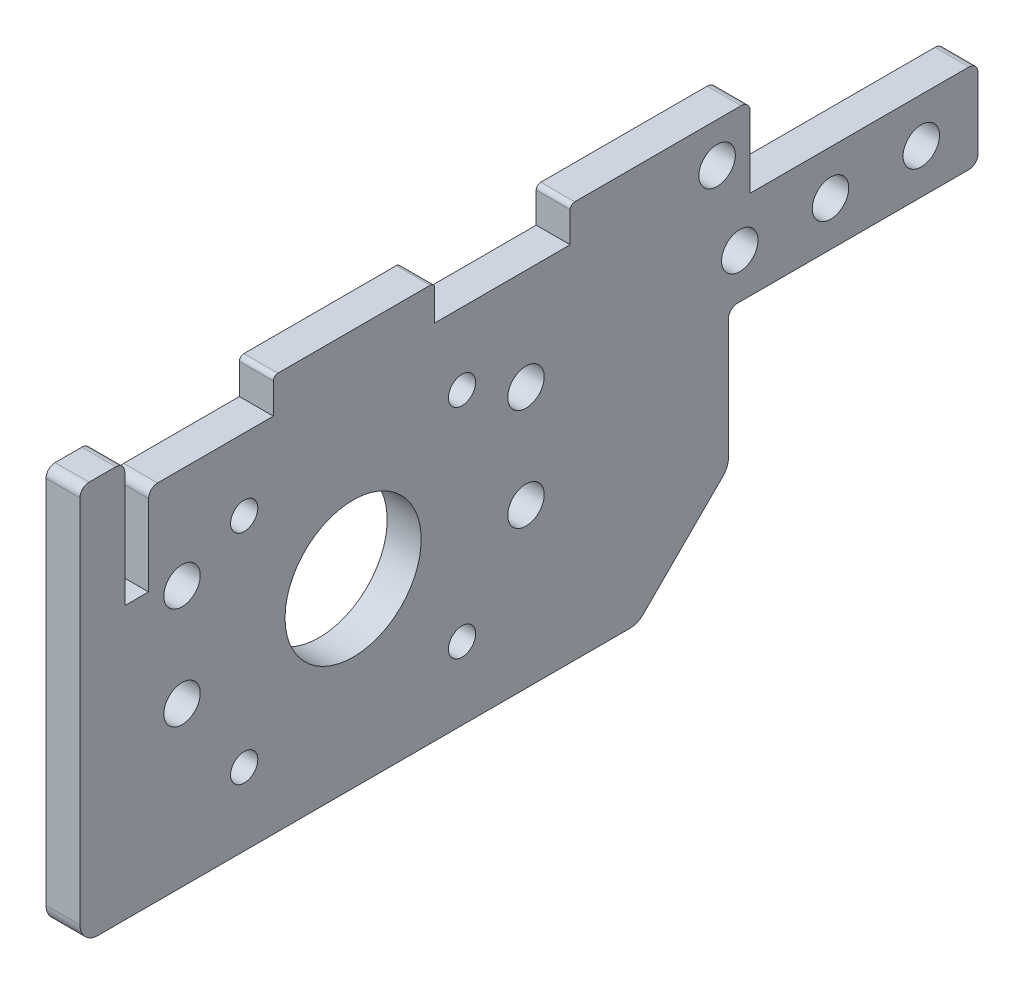
SolidWorks part; units mm, degrees
material "AISI Type A2 Tool Steel"
ref_plane "Front Plane" through (0, 0, 0) normal (0, 0, 1) x (1, 0, 0)
ref_plane "Top Plane" through (0, 0, 0) normal (0, 1, 0) x (1, 0, 0)
ref_plane "Right Plane" through (0, 0, 0) normal (1, 0, 0) x (0, 0, -1)
sketch "Top Layout" plane through (0, 0, 0) normal (0, 1, 0) x (1, 0, 0)
  line L0 (-114.046, -123.825) -> (-104.775, -123.825) construction
  line L1 (-104.775, -142.875) -> (-101.6, -142.875)
  line L2 (-104.775, -142.875) -> (-104.775, -104.775)
  line L3 (-104.775, -104.775) -> (-101.6, -104.775)
  line L4 (-101.6, -142.875) -> (-101.6, -104.775)
  line L5 (-104.775, -142.875) -> (-101.6, -104.775) construction
  line L6 (-104.775, -104.775) -> (-101.6, -142.875) construction
  line L7 (-19.05, -105.8164) -> (-101.6, -105.8164)
  line L8 (-19.05, -105.8164) -> (-19.05, -141.8336)
  line L9 (-19.05, -141.8336) -> (-101.6, -141.8336)
  line L10 (-101.6, -105.8164) -> (-101.6, -141.8336)
  line L11 (-19.05, -105.8164) -> (-101.6, -141.8336) construction
  line L12 (-19.05, -141.8336) -> (-101.6, -105.8164) construction
  line L13 (-133.096, -85.725) -> (-114.046, -85.725)
  line L14 (-133.096, -85.725) -> (-133.096, -161.925)
  line L15 (-133.096, -161.925) -> (-114.046, -161.925)
  line L16 (-114.046, -85.725) -> (-114.046, -161.925)
  line L17 (-133.096, -85.725) -> (-114.046, -161.925) construction
  line L18 (-133.096, -161.925) -> (-114.046, -85.725) construction
  line L19 (-104.775, -123.825) -> (0, -123.825) construction
  line L20 (0, -123.825) -> (0, 0) construction
  line L21 (-52.3528, -40.1717) -> (0, 0) construction
  line L22 (-70.6449, -16.3328) -> (-18.2922, 23.8388)
  line L23 (-34.0606, -64.0105) -> (18.2922, -23.8388)
  line L24 (-30.9251, 40.3023) -> (-122.2248, -29.7544)
  line L25 (-153.9748, -53.975) -> (-153.9748, -123.825)
  line L26 (-109.5248, -162.052) -> (109.5248, -162.052)
  line L27 (0, -162.052) -> (0, -123.825) construction
  line L28 (-109.5248, -162.052) -> (-109.5248, -20.0093) construction
  line L29 (-104.775, -142.875) -> (-104.775, -152.527)
  line L30 (-104.775, -152.527) -> (104.775, -152.527)
  line L31 (104.775, -104.775) -> (101.6, -104.775)
  line L32 (-144.4498, -73.025) -> (-109.5248, -73.025)
  line L33 (-144.4498, -73.025) -> (-144.4498, -123.825)
  line L34 (-144.4498, -123.825) -> (-109.5248, -123.825) construction
  line L35 (-109.5248, -73.025) -> (-109.5248, -162.052)
  line L36 (-144.4498, -73.025) -> (-109.5248, -123.825) construction
  line L37 (-144.4498, -123.825) -> (-109.5248, -73.025) construction
  line L38 (101.6, -142.875) -> (101.6, -104.775)
  line L39 (104.775, -142.875) -> (101.6, -142.875)
  line L40 (104.775, -142.875) -> (104.775, -104.775)
  line L41 (104.775, -142.875) -> (104.775, -152.527)
  line L42 (109.5248, -162.052) -> (109.5248, -20.0093) construction
  line L43 (30.9251, 40.3023) -> (122.2248, -29.7544)
  line L45 (19.05, -141.8336) -> (101.6, -141.8336)
  line L46 (101.6, -105.8164) -> (101.6, -141.8336)
  line L47 (19.05, -105.8164) -> (101.6, -105.8164)
  line L48 (19.05, -105.8164) -> (19.05, -141.8336)
  line L49 (133.096, -161.925) -> (114.046, -161.925)
  line L50 (114.046, -85.725) -> (114.046, -161.925)
  line L51 (133.096, -85.725) -> (114.046, -85.725)
  line L52 (133.096, -85.725) -> (133.096, -161.925)
  line L53 (144.4498, -123.825) -> (109.5248, -123.825) construction
  line L54 (109.5248, -73.025) -> (109.5248, -162.052)
  line L55 (144.4498, -73.025) -> (109.5248, -73.025)
  line L56 (144.4498, -73.025) -> (144.4498, -123.825)
  line L57 (-109.5248, -123.825) -> (-109.5248, -162.052) construction
  line L62 (-153.9748, -53.975) -> (-122.2248, -53.975)
  line L63 (-122.2248, -53.975) -> (-122.2248, -29.7544)
  line L64 (-144.4498, -123.825) -> (-153.9748, -123.825)
  line L65 (153.9748, -53.975) -> (153.9748, -123.825)
  line L66 (109.5248, -123.825) -> (109.5248, -162.052) construction
  line L67 (144.4498, -123.825) -> (153.9748, -123.825)
  line L68 (122.2248, -29.7544) -> (122.2248, -53.975)
  line L73 (-104.775, -104.775) -> (-104.775, -16.3647) construction
  line L74 (-95.25, -162.052) -> (-95.25, -9.0559) construction
  line L75 (-109.5248, -162.052) -> (-109.5248, -123.825) construction
  line L76 (109.5248, -162.052) -> (109.5248, -123.825) construction
  line L77 (122.2248, -53.975) -> (153.9748, -53.975)
  line L83 (104.775, -155.5496) -> (-104.775, -155.5496) construction
  line L88 (95.25, -162.052) -> (95.25, -9.0559) construction
  line L89 (104.775, -104.775) -> (104.775, -16.3647) construction
  line L92 (-104.775, -152.527) -> (-104.775, -162.052) construction
  line L93 (-14.605, -76.327) -> (14.605, -76.327)
  line L94 (-14.605, -76.327) -> (-14.605, -152.527)
  line L95 (-14.605, -152.527) -> (14.605, -152.527)
  line L96 (14.605, -76.327) -> (14.605, -152.527)
  line L97 (-14.605, -76.327) -> (14.605, -152.527) construction
  line L98 (-14.605, -152.527) -> (14.605, -76.327) construction
  line L99 (104.775, -152.527) -> (104.775, -162.052) construction
  line L100 (-19.05, -105.8164) -> (0, -105.8164) construction
  line L107 (0, -105.8164) -> (19.05, -105.8164) construction
  line L108 (104.775, -123.825) -> (114.046, -123.825) construction
  circle A0 centre (0, 0) radius 114.3
  circle A1 centre (0, 0) radius 6.35
  circle A2 centre (-52.3528, -40.1717) radius 17.8
  circle A3 centre (0, 0) radius 30.0482
  circle A4 centre (-52.3528, -40.1717) radius 30.0482
  arc A5 (-30.9251, 40.3023) -> (30.9251, 40.3023) centre (0, 0) cw
  point P2 (-103.1875, -123.825)
  point P7 (-60.325, -123.825)
  point P12 (-123.571, -123.825)
  point P30 (-126.9873, -98.425)
  point P35 (0, -114.427)
  point P53 (0, -152.527)
  dimension "D1" = 35.6
  dimension "D2" = 12.7
  dimension "D3" = 228.6
  dimension "D11" = 60.0964
  dimension "D12" = 50.8
  dimension "D14" = 52.5
  dimension "D4" = 3.175
  dimension "D5" = 19.05
  dimension "D6" = 76.2
  dimension "D7" = 82.55
  dimension "D8" = 38.1
  dimension "D9" = 104.775
  dimension "D10" = 18.0086
  dimension "D13" = 9.525
  dimension "D15" = 4.7498
  dimension "D16" = 9.525
  dimension "D17" = 9.652
  dimension "D18" = 50.8
  dimension "D19" = 12.446
  dimension "D20" = 65.9892
  dimension "D21" = 19.05
  dimension "D22" = 34.925
  dimension "D23" = 123.825
  dimension "D24" = 12.7
  dimension "D25" = 9.525
  dimension "D26" = 29.21
  dimension "D27" = 76.2
  dimension "D28" = 3.0226
sketch "Side Layout" plane through (0, 0, 0) normal (1, 0, 0) x (0, 0, -1)
  line L0 (0, -38.1) -> (0, 33.7344) construction
  line L1 (-114.3, -20.955) -> (114.3, -20.955)
  line L2 (-114.3, -20.955) -> (-114.3, -33.655)
  line L3 (-114.3, -33.655) -> (114.3, -33.655)
  line L4 (114.3, -20.955) -> (114.3, -33.655)
  line L5 (-114.3, -20.955) -> (114.3, -33.655) construction
  line L6 (-114.3, -33.655) -> (114.3, -20.955) construction
  line L7 (-9.525, -32.9406) -> (9.525, -32.9406)
  line L8 (-9.525, -32.9406) -> (-9.525, -38.1)
  line L9 (-9.525, -38.1) -> (9.525, -38.1)
  line L10 (9.525, -32.9406) -> (9.525, -38.1)
  line L11 (-9.525, -32.9406) -> (9.525, -38.1) construction
  line L12 (-9.525, -38.1) -> (9.525, -32.9406) construction
  line L13 (-11.9126, -29.3338) -> (11.9126, -29.3338)
  line L14 (-11.9126, -29.3338) -> (-11.9126, -32.9406)
  line L15 (-11.9126, -32.9406) -> (11.9126, -32.9406)
  line L16 (11.9126, -29.3338) -> (11.9126, -32.9406)
  line L17 (-11.9126, -29.3338) -> (11.9126, -32.9406) construction
  line L18 (-11.9126, -32.9406) -> (11.9126, -29.3338) construction
  line L19 (-6.35, -32.9406) -> (6.35, -32.9406)
  line L20 (-6.35, -32.9406) -> (-6.35, 33.7344)
  line L21 (-6.35, 33.7344) -> (6.35, 33.7344)
  line L22 (6.35, -32.9406) -> (6.35, 33.7344)
  line L23 (-6.35, -32.9406) -> (6.35, 33.7344) construction
  line L24 (-6.35, 33.7344) -> (6.35, -32.9406) construction
  line L25 (-162.052, 0) -> (-123.825, 0) construction
  line L26 (114.3, -33.655) -> (114.3, 0) construction
  line L27 (-142.875, 19.05) -> (-104.775, 19.05)
  line L28 (-40.1717, -9.525) -> (-40.1717, 5.4) construction
  line L29 (-142.875, 19.05) -> (-142.875, -19.05)
  line L30 (-142.875, -19.05) -> (-104.775, -19.05)
  line L31 (-104.775, 19.05) -> (-104.775, -19.05)
  line L32 (-142.875, 19.05) -> (-104.775, -19.05) construction
  line L33 (-142.875, -19.05) -> (-104.775, 19.05) construction
  line L34 (-130.175, -38.1) -> (-117.9516, -38.1) construction
  line L35 (-57.9717, -14.6) -> (-22.3717, -14.6)
  line L36 (-30.0482, -2.794) -> (30.0482, -2.794)
  line L37 (-30.0482, -2.794) -> (-30.0482, -20.955)
  line L38 (-30.0482, -20.955) -> (30.0482, -20.955)
  line L39 (30.0482, -2.794) -> (30.0482, -20.955)
  line L40 (-30.0482, -2.794) -> (30.0482, -20.955) construction
  line L41 (-30.0482, -20.955) -> (30.0482, -2.794) construction
  line L42 (-30.0482, -2.794) -> (-30.0482, 0) construction
  line L43 (-123.825, 0) -> (0, 0) construction
  line L44 (-57.9717, -14.6) -> (-57.9717, 25.4)
  line L45 (-57.9717, 25.4) -> (-22.3717, 25.4)
  line L46 (-22.3717, -14.6) -> (-22.3717, 25.4)
  line L47 (-19.05, 0) -> (19.05, 0)
  line L48 (-19.05, 0) -> (-19.05, -1.9812)
  line L49 (-19.05, -1.9812) -> (19.05, -1.9812)
  line L50 (19.05, 0) -> (19.05, -1.9812)
  line L51 (-19.05, 0) -> (19.05, -1.9812) construction
  line L52 (-19.05, -1.9812) -> (19.05, 0) construction
  line L53 (-70.2199, -3.175) -> (-10.1235, -3.175)
  line L54 (-70.2199, -3.175) -> (-70.2199, -15.875)
  line L55 (-70.2199, -15.875) -> (-10.1235, -15.875)
  line L56 (-10.1235, -3.175) -> (-10.1235, -15.875)
  line L57 (-70.2199, -3.175) -> (-10.1235, -15.875) construction
  line L58 (-70.2199, -15.875) -> (-10.1235, -3.175) construction
  line L59 (-40.1717, -9.525) -> (-40.1717, 0) construction
  line L60 (-57.9717, -14.6) -> (-22.3717, 25.4) construction
  line L61 (-57.9717, 25.4) -> (-22.3717, -14.6) construction
  line L62 (-22.3717, 0) -> (-57.9717, 0) construction
  line L63 (-137.8162, 0) -> (-123.825, -13.9912) construction
  line L64 (-139.065, 15.24) -> (-108.585, 15.24) construction
  line L65 (-139.065, 15.24) -> (-139.065, -15.24) construction
  line L66 (-139.065, -15.24) -> (-108.585, -15.24) construction
  line L67 (-108.585, 15.24) -> (-108.585, -15.24) construction
  line L68 (-139.065, 15.24) -> (-108.585, -15.24) construction
  line L69 (-139.065, -15.24) -> (-108.585, 15.24) construction
  line L70 (-137.8162, 0) -> (-123.825, 13.9912) construction
  line L71 (-123.825, -13.9912) -> (-109.8338, 0) construction
  line L72 (-123.825, 13.9912) -> (-109.8338, 0) construction
  line L73 (-137.8162, 0) -> (-109.8338, 0) construction
  line L74 (-123.825, -13.9912) -> (-123.825, 13.9912) construction
  line L75 (-6.35, 17.8594) -> (6.35, 17.8594)
  line L76 (114.3, 0) -> (-114.3, 0) construction
  line L77 (-22.3717, 19.05) -> (-6.35, 19.05) construction
  line L78 (-123.825, 38.1) -> (-97.9206, 38.1) construction
  line L79 (-19.05, -3.5814) -> (19.05, -3.5814)
  line L80 (-19.05, -3.5814) -> (-19.05, -1.9812)
  line L81 (-19.05, -1.9812) -> (19.05, -1.9812)
  line L82 (19.05, -3.5814) -> (19.05, -1.9812)
  line L83 (-19.05, -3.5814) -> (19.05, -1.9812) construction
  line L84 (-19.05, -1.9812) -> (19.05, -3.5814) construction
  line L85 (-8.7376, -16.7608) -> (8.7376, -16.7608)
  line L86 (-8.7376, -16.7608) -> (-8.7376, -29.3338)
  line L87 (-8.7376, -29.3338) -> (8.7376, -29.3338)
  line L88 (8.7376, -16.7608) -> (8.7376, -29.3338)
  line L89 (-8.7376, -16.7608) -> (8.7376, -29.3338) construction
  line L90 (-8.7376, -29.3338) -> (8.7376, -16.7608) construction
  line L91 (-8.7376, -3.5814) -> (8.7376, -3.5814)
  line L92 (-8.7376, -3.5814) -> (-8.7376, -16.1544)
  line L93 (-8.7376, -16.1544) -> (8.7376, -16.1544)
  line L94 (8.7376, -3.5814) -> (8.7376, -16.1544)
  line L95 (-8.7376, -3.5814) -> (8.7376, -16.1544) construction
  line L96 (-8.7376, -16.1544) -> (8.7376, -3.5814) construction
  circle A0 centre (-123.825, 0) radius 18.0086
  circle A1 centre (-123.825, 0) radius 38.1
  circle A2 centre (-139.065, 15.24) radius 1.905
  circle A3 centre (-108.585, 15.24) radius 1.905
  circle A4 centre (-108.585, -15.24) radius 1.905
  circle A5 centre (-139.065, -15.24) radius 1.905
  circle A6 centre (-137.8162, 0) radius 1.6002
  circle A7 centre (-123.825, 13.9912) radius 1.6002
  circle A8 centre (-109.8338, 0) radius 1.6002
  circle A9 centre (-123.825, -13.9912) radius 1.6002
  point P0 (0, -27.305)
  point P6 (0, -31.1372)
  point P7 (0, -35.5203)
  point P21 (0, 0.3969)
  point P32 (0, -11.8745)
  point P43 (0, -0.9906)
  point P55 (-40.1717, -9.525)
  point P72 (-40.1717, 5.4)
  point P88 (0, -23.0473)
  point P93 (0, -2.7813)
  point P102 (0, -9.8679)
  dimension "D17" = 3.81
  dimension "D18" = 3.2004
  dimension "D1" = 12.7
  dimension "D2" = 5.1594
  dimension "D3" = 19.05
  dimension "D4" = 3.6068
  dimension "D5" = 23.8252
  dimension "D6" = 12.7
  dimension "D7" = 18.161
  dimension "D8" = 1.9812
  dimension "D9" = 12.7
  dimension "D10" = 40
  dimension "D11" = 25.4
  dimension "D12" = 50.8
  dimension "D13" = 41.275
  dimension "D14" = 30.48
  dimension "D15" = 4.445
  dimension "D16" = 19.7866
  dimension "D19" = 15.875
  dimension "D20" = 6.35
  dimension "D21" = 38.1
  dimension "D22" = 1.6002
  dimension "D23" = 38.1
  dimension "D24" = 17.4752
  dimension "D25" = 12.573
ref_plane "Plane1" through (0, 25.4, 0) normal (0, 1, 0) x (1, 0, 0)
sketch "Sketch3" plane through (0, 25.4, 0) normal (0, 1, 0) x (1, 0, 0)
  line L0 (-104.775, -36.3747) -> (-30.9251, 20.2924)
  line L1 (-104.775, -104.775) -> (-104.775, -16.3647) construction
  line L2 (0, -200130.175) -> (0, 199882.0484) construction
  line L3 (-30.9251, 40.3023) -> (-122.2248, -29.7544) construction
  line L5 (-104.775, -36.3747) -> (-104.775, -77.6497)
  line L6 (-92.075, -77.6497) -> (-104.775, -77.6497)
  line L7 (30.9251, 20.2924) -> (104.775, -36.3747)
  line L8 (104.775, -77.6497) -> (92.075, -77.6497)
  line L9 (104.775, -36.3747) -> (104.775, -77.6497)
  line L11 (104.775, -104.775) -> (104.775, -16.3647) construction
  line L12 (30.9251, 40.3023) -> (122.2248, -29.7544) construction
  line L13 (92.075, -74.6536) -> (24.1423, -22.5271)
  line L14 (-32.2514, -66.3682) -> (20.1013, -26.1965)
  line L15 (-30.9251, 20.2924) -> (0, 44.022)
  line L16 (0, 44.022) -> (30.9251, 20.2924)
  line L17 (-92.075, -77.6497) -> (-92.075, -73.1917)
  line L19 (-92.075, -73.1917) -> (-52.3528, -73.1917)
  line L20 (92.075, -74.6536) -> (92.075, -77.6497)
  circle A0 centre (-52.3528, -40.1717) radius 17.8 construction
  circle A1 centre (-52.3528, -40.1717) radius 17.8
  circle A2 centre (0, 0) radius 6.35
  circle A3 centre (0, 0) radius 6.35 construction
  arc A4 (-52.3528, -73.1917) -> (-32.2514, -66.3682) centre (-52.3528, -40.1717) ccw
  arc A5 (20.1013, -26.1965) -> (24.1423, -22.5271) centre (0, 0) ccw
  arc A6 (30.9251, 20.2924) -> (-30.9251, 20.2924) centre (0, -20.01) ccw construction
  point P28 (0, 44.022)
  dimension "D1" = 33.02
  dimension "D5" = 50.8
  dimension "D2" = 41.275
  dimension "D3" = 34.925
  dimension "D4" = 12.7
  dimension "D6" = 38.1
ref_plane "Plane3" through (-104.775, 0, 0) normal (-1, 0, 0) x (0, 0, 1)
sketch "Sketch6" plane through (-104.775, 0, 0) normal (-1, 0, 0) x (0, 0, 1)
  line L0 (162.052, -25.4) -> (162.052, 25.4)
  line L1 (162.052, 25.4) -> (77.6497, 25.4)
  line L2 (36.3747, 25.4) -> (77.6497, 25.4) construction
  line L3 (147.7645, 11.1125) -> (162.052, 11.1125) construction
  line L4 (162.052, 0) -> (71.2997, 0) construction
  line L5 (77.6497, 25.4) -> (77.6497, 19.05)
  line L6 (77.6497, 19.05) -> (36.3747, 19.05)
  line L7 (36.3747, 19.05) -> (36.3747, 6.35)
  line L8 (36.3747, 6.35) -> (71.2997, 6.35)
  line L10 (99.6315, -3.175) -> (99.6315, 11.1125) construction
  line L11 (71.2997, -25.4) -> (162.052, -25.4)
  line L13 (71.2997, 6.35) -> (71.2997, -25.4)
  line L14 (152.527, -25.4) -> (152.527, 25.4) construction
  line L15 (99.6315, 11.1125) -> (99.6315, 25.4) construction
  line L16 (147.7645, 11.1125) -> (147.7645, 25.4) construction
  line L17 (94.869, -7.9375) -> (104.394, -7.9375) construction
  line L18 (94.869, -7.9375) -> (94.869, 25.4) construction
  line L19 (94.869, 25.4) -> (104.394, 25.4) construction
  line L20 (104.394, -7.9375) -> (104.394, 25.4) construction
  line L21 (94.869, -7.9375) -> (104.394, 25.4) construction
  line L22 (94.869, 25.4) -> (104.394, -7.9375) construction
  line L23 (147.7645, 11.1125) -> (147.7645, -3.175) construction
  line L24 (104.394, -7.9375) -> (123.825, -7.9375) construction
  line L25 (143.002, -7.9375) -> (152.527, -7.9375) construction
  line L26 (143.002, -7.9375) -> (143.002, 25.4) construction
  line L27 (143.002, 25.4) -> (152.527, 25.4) construction
  line L28 (152.527, -7.9375) -> (152.527, 25.4) construction
  line L29 (143.002, -7.9375) -> (152.527, 25.4) construction
  line L30 (143.002, 25.4) -> (152.527, -7.9375) construction
  line L31 (123.825, -7.9375) -> (152.527, -7.9375) construction
  line L32 (104.775, 19.05) -> (104.775, -19.05) construction
  line L34 (155.702, -25.4) -> (155.702, 25.4) construction
  circle A0 centre (109.8338, 0) radius 1.6002 construction
  circle A1 centre (123.825, 13.9912) radius 1.6002 construction
  circle A2 centre (137.8162, 0) radius 1.6002 construction
  circle A3 centre (123.825, -13.9912) radius 1.6002 construction
  circle A4 centre (109.8338, 0) radius 1.6002 construction
  circle A5 centre (123.825, 13.9912) radius 1.6002 construction
  circle A6 centre (137.8162, 0) radius 1.6002 construction
  circle A7 centre (123.825, -13.9912) radius 1.6002 construction
  circle A8 centre (123.825, 0) radius 18.0086 construction
  circle A9 centre (123.825, 0) radius 18.0086 construction
  circle A10 centre (123.825, 0) radius 9.525
  circle A11 centre (108.585, -15.24) radius 1.905 construction
  circle A12 centre (108.585, 15.24) radius 1.905 construction
  circle A13 centre (139.065, 15.24) radius 1.905 construction
  circle A14 centre (139.065, -15.24) radius 1.905 construction
  circle A15 centre (108.585, -15.24) radius 1.905
  circle A16 centre (108.585, 15.24) radius 1.905
  circle A17 centre (139.065, 15.24) radius 1.905
  circle A18 centre (139.065, -15.24) radius 1.905
  circle A19 centre (147.7645, 11.1125) radius 2.5527
  circle A26 centre (99.6315, 11.1125) radius 2.5527
  circle A27 centre (99.6315, -3.175) radius 2.5527
  circle A28 centre (147.7645, -3.175) radius 2.5527
  point P29 (0, 0)
  point P55 (99.6315, 8.7312)
  point P61 (147.7645, 8.7312)
  dimension "D4" = 19.05
  dimension "D7" = 5.1054
  dimension "D1" = 6.35
  dimension "D2" = 12.7
  dimension "D3" = 25.4
  dimension "D5" = 6.35
  dimension "D6" = 3.175
  dimension "D8" = 0.381
  dimension "D9" = 14.2875
  dimension "D10" = 9.525
  dimension "D12" = 33.3375
extrude "Side Plate Extrude" add sketch "Sketch6" along normal up to vertex (4.7498 mm away) up to point (-109.5248, 0, 73.025)
sketch "Sketch12" [suppressed] plane through (0, 19.05, 0) normal (0, 1, 0) x (1, 0, 0)
  line L0 (-104.775, -77.6497) -> (-104.775, -36.3747)
  line L1 (-104.775, -36.3747) -> (-92.075, -36.3747)
  line L3 (-92.075, -36.3747) -> (-92.075, -77.6497)
  line L5 (-92.075, -77.6497) -> (-104.775, -77.6497)
  line L6 (-98.425, -77.6497) -> (-98.425, -63.3622) construction
  line L7 (-98.425, -63.3622) -> (-98.425, -50.6622) construction
  line L8 (-98.425, -50.6622) -> (-98.425, -36.3747) construction
  line L10 (-98.425, -36.3747) -> (-104.775, -36.3747) construction
  circle A0 centre (-98.425, -63.3622) radius 2.5527
  circle A1 centre (-98.425, -50.6622) radius 2.5527
  dimension "D2" = 5.1054
  dimension "D1" = 12.7
  dimension "D3" = 12.7
sketch "Sketch15" plane through (-109.5248, 0, 0) normal (-1, 0, 0) x (0, 0, 1)
  line L0 (36.3747, 12.7) -> (44.3122, 12.7) construction
  line L1 (36.3747, 19.05) -> (36.3747, 6.35) construction
  line L2 (44.3122, 12.7) -> (57.0122, 12.7) construction
  line L3 (57.0122, 12.7) -> (69.7122, 12.7) construction
  line L4 (69.7122, 12.7) -> (77.6497, 12.7) construction
  line L5 (77.6497, 12.7) -> (77.6497, 19.05) construction
  circle A0 centre (44.3122, 12.7) radius 2.5527
  circle A1 centre (57.0122, 12.7) radius 2.5527
  circle A2 centre (69.7122, 12.7) radius 2.5527
  dimension "D1" = 5.1054
  dimension "D2" = 12.7
extrude "Custom Nutstrip Holes" cut sketch "Sketch15" against normal through all
ref_plane "Plane5" through (0, 0, 152.527) normal (0, 0, 1) x (1, 0, 0)
sketch "Sketch41" plane through (0, 0, 152.527) normal (0, 0, 1) x (1, 0, 0)
  line L0 (-104.775, -7.9375) -> (-104.775, 25.4) construction
  line L1 (-104.775, -7.9375) -> (-104.775, 12.7)
  line L2 (-104.775, -7.9375) -> (104.775, -7.9375)
  line L3 (104.775, -7.9375) -> (104.775, 12.7)
  line L4 (104.775, 25.4) -> (-104.775, 25.4)
  line L5 (0, -7.9375) -> (0, 25.4) construction
  line L6 (-104.775, 3.9624) -> (-100.0125, 3.9624) construction
  line L7 (-100.0125, 3.9624) -> (-100.0125, 25.4) construction
  line L8 (104.775, 3.9624) -> (100.0125, 3.9624) construction
  line L9 (100.0125, 3.9624) -> (100.0125, 25.4) construction
  line L10 (19.05, 20.6375) -> (23.8252, 20.6375) construction
  line L11 (19.05, 15.875) -> (78.5876, 15.875) construction
  line L12 (19.05, 15.875) -> (19.05, 25.4) construction
  line L13 (19.05, 25.4) -> (78.5876, 25.4) construction
  line L14 (78.5876, 15.875) -> (78.5876, 25.4) construction
  line L15 (19.05, 15.875) -> (78.5876, 25.4) construction
  line L16 (19.05, 25.4) -> (78.5876, 15.875) construction
  line L17 (23.8252, 20.6375) -> (38.1127, 20.6375) construction
  line L18 (38.1127, 20.6375) -> (52.4002, 20.6375) construction
  line L19 (52.4002, 20.6375) -> (66.6877, 20.6375) construction
  line L20 (-104.775, 25.4) -> (-112.395, 25.4)
  line L21 (-112.395, 25.4) -> (-112.395, 3.175)
  line L22 (-112.395, 3.175) -> (-109.5248, 3.175)
  line L23 (-109.5248, 3.175) -> (-109.5248, 12.7)
  line L24 (-109.5248, 12.7) -> (-104.775, 12.7)
  line L25 (-104.775, 12.7) -> (-104.775, 25.4) construction
  line L26 (104.775, 25.4) -> (112.395, 25.4)
  line L27 (112.395, 25.4) -> (112.395, 3.175)
  line L28 (112.395, 3.175) -> (109.5248, 3.175)
  line L29 (109.5248, 3.175) -> (109.5248, 12.7)
  line L30 (109.5248, 12.7) -> (104.775, 12.7)
  line L31 (104.775, 12.7) -> (104.775, 25.4) construction
  line L32 (-100.0125, 3.9624) -> (-87.3125, 3.9624) construction
  line L33 (-63.5, -1.5875) -> (0, -1.5875) construction
  line L34 (0, -1.5875) -> (63.5, -1.5875) construction
  line L35 (63.5, -1.5875) -> (63.5, -7.9375) construction
  circle A0 centre (-100.0125, 3.9624) radius 2.5527
  circle A1 centre (100.0125, 3.9624) radius 2.5527
  circle A2 centre (23.8252, 20.6375) radius 2.5527
  circle A3 centre (38.1127, 20.6375) radius 2.5527
  circle A4 centre (52.4002, 20.6375) radius 2.5527
  circle A5 centre (66.6877, 20.6375) radius 2.5527
  circle A6 centre (-66.6877, 20.6375) radius 2.5527
  circle A7 centre (-52.4002, 20.6375) radius 2.5527
  circle A8 centre (-38.1127, 20.6375) radius 2.5527
  circle A9 centre (-23.8252, 20.6375) radius 2.5527
  circle A10 centre (-87.3125, 3.9624) radius 2.5527
  circle A11 centre (87.3125, 3.9624) radius 2.5527
  circle A12 centre (-63.5, -1.5875) radius 2.5527
  circle A13 centre (63.5, -1.5875) radius 2.5527
  point P14 (48.8188, 20.6375)
  dimension "D3" = 5.1054
  dimension "D7" = 5.1054
  dimension "D1" = 21.4376
  dimension "D2" = 4.7625
  dimension "D4" = 9.525
  dimension "D5" = 59.5376
  dimension "D6" = 4.7752
  dimension "D8" = 14.2875
  dimension "D9" = 7.62
  dimension "D10" = 4.7498
  dimension "D11" = 12.7
  dimension "D12" = 9.525
  dimension "D13" = 19.05
  dimension "D14" = 12.7
  dimension "D15" = 6.35
  dimension "D16" = 63.5
sketch "Sketch43" plane through (-109.5248, 0, 0) normal (-1, 0, 0) x (0, 0, 1)
  line L1 (152.527, 12.7) -> (155.702, 12.7)
  line L2 (152.527, 12.7) -> (152.527, 25.4)
  line L3 (152.527, 25.4) -> (155.702, 25.4)
  line L4 (155.702, 12.7) -> (155.702, 25.4)
  line L5 (152.527, 12.7) -> (155.702, 25.4) construction
  line L6 (152.527, 25.4) -> (155.702, 12.7) construction
  line L7 (162.052, 25.4) -> (77.6497, 25.4) construction
  point P4 (154.1145, 19.05)
  dimension "D1" = 3.175
extrude "Cut-Extrude19" cut sketch "Sketch43" against normal through all
sketch "Sketch44" plane through (0, 25.4, 0) normal (0, 1, 0) x (1, 0, 0)
  line L0 (73.8315, -147.7645) -> (73.8315, -152.527) construction
  line L1 (92.075, -74.6536) -> (92.075, -77.6497) construction
  line L2 (-92.075, -77.6497) -> (-92.075, -73.1917) construction
  line L3 (0, -123.825) -> (0, 0) construction
  line L4 (-92.075, -73.1917) -> (-52.3528, -73.1917) construction
  line L5 (-104.775, -104.775) -> (-104.775, -16.3647) construction
  line L6 (-32.2514, -66.3682) -> (20.1013, -26.1965) construction
  line L21 (-104.775, -68.1247) -> (-104.775, -152.527)
  line L22 (-104.775, -152.527) -> (104.775, -152.527)
  line L23 (104.775, -152.527) -> (104.775, -68.1247)
  line L34 (-104.775, -99.6315) -> (-100.0125, -99.6315) construction
  line L35 (-104.775, -147.7645) -> (-100.0125, -147.7645) construction
  line L36 (0, -152.527) -> (0, -35.6178) construction
  line L38 (30.969, -147.7645) -> (45.2565, -147.7645) construction
  line L39 (45.2565, -147.7645) -> (59.544, -147.7645) construction
  line L40 (59.544, -147.7645) -> (73.8315, -147.7645) construction
  line L41 (23.8252, -152.527) -> (30.969, -152.527) construction
  line L42 (104.775, -152.527) -> (-104.775, -152.527) construction
  line L43 (30.969, -152.527) -> (38.1127, -152.527) construction
  line L44 (30.969, -152.527) -> (30.969, -147.7645) construction
  line L45 (-92.075, -77.6497) -> (-104.775, -77.6497) construction
  line L48 (-35.1507, -62.5899) -> (-8.9743, -42.504) construction
  line L49 (-8.9743, -42.504) -> (17.2021, -22.4182) construction
  line L50 (45.5313, -32.9364) -> (87.3125, -64.9962) construction
  line L51 (92.075, -74.6536) -> (24.1423, -22.5271) construction
  line L52 (104.775, -77.6497) -> (92.075, -77.6497) construction
  line L79 (-104.775, -68.1247) -> (-92.075, -68.1247)
  line L80 (-92.075, -68.1247) -> (-92.075, -63.6667)
  line L85 (21.8118, -8.7328) -> (92.075, -62.6476)
  line L86 (-38.0499, -58.8115) -> (14.3028, -18.6398)
  line L87 (-92.075, -63.6667) -> (-52.3528, -63.6667)
  line L88 (92.075, -62.6476) -> (92.075, -68.1247)
  line L89 (92.075, -68.1247) -> (104.775, -68.1247)
  circle A0 centre (-73.8315, -147.7645) radius 2.5527
  circle A1 centre (-59.544, -147.7645) radius 2.5527
  circle A2 centre (-45.2565, -147.7645) radius 2.5527
  circle A3 centre (-30.969, -147.7645) radius 2.5527
  circle A17 centre (-100.0125, -99.6315) radius 2.5527
  circle A18 centre (-100.0125, -147.7645) radius 2.5527
  circle A19 centre (100.0125, -147.7645) radius 2.5527
  circle A20 centre (100.0125, -99.6315) radius 2.5527
  circle A21 centre (30.969, -147.7645) radius 2.5527
  circle A22 centre (45.2565, -147.7645) radius 2.5527
  circle A23 centre (59.544, -147.7645) radius 2.5527
  circle A24 centre (73.8315, -147.7645) radius 2.5527
  circle A25 centre (-87.3125, -68.4292) radius 4.7625 construction
  circle A26 centre (-35.1507, -62.5899) radius 4.7625 construction
  circle A27 centre (-8.9743, -42.504) radius 4.7625 construction
  circle A28 centre (17.2021, -22.4182) radius 4.7625 construction
  circle A29 centre (45.5313, -32.9364) radius 4.7625 construction
  circle A30 centre (87.3125, -64.9962) radius 4.7625 construction
  circle A32 centre (-87.3125, -68.4292) radius 2.5527
  circle A33 centre (-35.1507, -62.5899) radius 2.5527
  circle A34 centre (-8.9743, -42.504) radius 2.5527 construction
  circle A35 centre (17.2021, -22.4182) radius 2.5527
  circle A36 centre (45.5313, -32.9364) radius 2.5527
  circle A37 centre (87.3125, -64.9962) radius 2.5527
  circle A38 centre (-97.155, -85.2697) radius 7.62 construction
  circle A39 centre (97.155, -85.2697) radius 7.62 construction
  circle A40 centre (24.5121, -32.4156) radius 7.62 construction
  arc A41 (20.1013, -26.1965) -> (24.1423, -22.5271) centre (0, 0) ccw construction
  circle A42 centre (-97.155, -85.2697) radius 2.5527
  circle A43 centre (24.5121, -32.4156) radius 2.5527
  circle A44 centre (97.155, -85.2697) radius 2.5527
  arc A56 (14.3028, -18.6398) -> (21.8118, -8.7328) centre (0, 0) ccw
  arc A57 (-52.3528, -63.6667) -> (-38.0499, -58.8115) centre (-52.3528, -40.1717) ccw
  point P4 (-104.775, -152.527)
  dimension "D2" = 5.1054
  dimension "D7" = 5.1054
  dimension "D8" = 15.24
  dimension "D3" = 9.525
  dimension "D9" = 9.525
  dimension "D4" = 4.7625
  dimension "D5" = 14.2875
  dimension "D6" = 9.525
  dimension "D1" = 4.7625
  dimension "D10" = 52.664
sketch "Sketch72" plane through (0, 25.4, 0) normal (0, 1, 0) x (1, 0, 0)
  line L0 (-104.775, -68.1247) -> (-104.775, -152.527) construction
  line L1 (-104.775, -152.527) -> (-109.5248, -152.527)
  line L2 (-104.775, -152.527) -> (-104.775, -135.0645)
  line L3 (-104.775, -135.0645) -> (-109.5248, -135.0645)
  line L4 (-109.5248, -152.527) -> (-109.5248, -135.0645)
  line L5 (-104.775, -152.527) -> (-109.5248, -135.0645) construction
  line L6 (-104.775, -135.0645) -> (-109.5248, -152.527) construction
  line L7 (-104.775, -152.527) -> (104.775, -152.527) construction
  line L8 (-77.0065, -152.527) -> (-73.8315, -147.7645) construction
  line L9 (-77.0065, -152.527) -> (-27.794, -152.527)
  line L10 (-77.0065, -152.527) -> (-77.0065, -155.5496)
  line L11 (-77.0065, -155.5496) -> (-27.794, -155.5496)
  line L12 (-27.794, -152.527) -> (-27.794, -155.5496)
  line L13 (-77.0065, -152.527) -> (-27.794, -155.5496) construction
  line L14 (-77.0065, -155.5496) -> (-27.794, -152.527) construction
  line L15 (-27.794, -152.527) -> (-30.969, -147.7645) construction
  line L16 (-77.0065, -152.527) -> (-77.0065, -147.7645) construction
  line L18 (-104.775, -93.5247) -> (-109.5248, -93.5247)
  line L19 (-104.775, -93.5247) -> (-104.775, -112.3315)
  line L20 (-104.775, -112.3315) -> (-109.5248, -112.3315)
  line L21 (-109.5248, -93.5247) -> (-109.5248, -112.3315)
  line L22 (-104.775, -93.5247) -> (-109.5248, -112.3315) construction
  line L23 (-104.775, -112.3315) -> (-109.5248, -93.5247) construction
  line L24 (0, -152.527) -> (-12.7, -152.527)
  line L25 (0, -152.527) -> (0, -155.5496)
  line L26 (0, -155.5496) -> (-12.7, -155.5496)
  line L27 (-12.7, -152.527) -> (-12.7, -155.5496)
  line L28 (0, -152.527) -> (-12.7, -155.5496) construction
  line L29 (0, -155.5496) -> (-12.7, -152.527) construction
  line L30 (-104.775, -68.1247) -> (-109.5248, -68.1247)
  line L31 (-104.775, -68.1247) -> (-104.775, -77.6497)
  line L32 (-104.775, -77.6497) -> (-109.5248, -77.6497)
  line L33 (-109.5248, -68.1247) -> (-109.5248, -77.6497)
  line L34 (-104.775, -68.1247) -> (-109.5248, -77.6497) construction
  line L35 (-104.775, -77.6497) -> (-109.5248, -68.1247) construction
  line L38 (-103.505, -155.5496) -> (-90.805, -155.5496)
  line L39 (-90.805, -152.527) -> (-90.805, -155.5496)
  line L40 (-103.505, -155.5496) -> (-103.505, -152.527)
  line L41 (-103.505, -155.5496) -> (-90.805, -152.527) construction
  line L42 (-103.505, -152.527) -> (-90.805, -152.527)
  line L43 (-77.0065, -147.7645) -> (-73.8315, -147.7645) construction
  line L44 (-103.505, -152.527) -> (-101.5221, -149.823) construction
  circle A0 centre (-100.0125, -147.7645) radius 2.5527 construction
  circle A1 centre (-73.8315, -147.7645) radius 2.5527 construction
  circle A2 centre (-30.969, -147.7645) radius 2.5527 construction
  point P4 (-107.1499, -143.7958)
  point P5 (-100.0125, -147.7645)
  point P16 (-52.4002, -154.0383)
  point P18 (-97.155, -154.0383)
  point P25 (-107.1499, -102.9281)
  point P34 (-6.35, -154.0383)
  point P39 (-107.1499, -72.8872)
  dimension "D1" = 4.7498
  dimension "D2" = 12.7
  dimension "D3" = 12.7
  dimension "D4" = 12.7
  dimension "D5" = 9.525
  dimension "D6" = 15.875
  dimension "D7" = 12.7
  dimension "D8" = 3.175
  dimension "D9" = 1.27
  dimension "D10" = 3.0226
sketch "Sketch73" plane through (-109.5248, 0, 0) normal (-1, 0, 0) x (0, 0, 1)
  line L1 (77.6497, 25.4) -> (93.5247, 25.4)
  line L2 (77.6497, 25.4) -> (77.6497, 30.1625)
  line L3 (77.6497, 30.1625) -> (93.5247, 30.1625)
  line L4 (93.5247, 25.4) -> (93.5247, 30.1625)
  line L5 (77.6497, 25.4) -> (93.5247, 30.1625) construction
  line L6 (77.6497, 30.1625) -> (93.5247, 25.4) construction
  line L7 (112.3315, 25.4) -> (135.0645, 25.4)
  line L8 (112.3315, 25.4) -> (112.3315, 30.1625)
  line L9 (112.3315, 30.1625) -> (135.0645, 30.1625)
  line L10 (135.0645, 25.4) -> (135.0645, 30.1625)
  line L11 (112.3315, 25.4) -> (135.0645, 30.1625) construction
  line L12 (112.3315, 30.1625) -> (135.0645, 25.4) construction
  line L13 (155.702, 25.4) -> (162.052, 25.4)
  line L14 (155.702, 25.4) -> (155.702, 30.1625)
  line L15 (155.702, 30.1625) -> (162.052, 30.1625)
  line L16 (162.052, 25.4) -> (162.052, 30.1625)
  line L17 (155.702, 25.4) -> (162.052, 30.1625) construction
  line L18 (155.702, 30.1625) -> (162.052, 25.4) construction
  point P4 (85.5872, 27.7812)
  point P10 (123.698, 27.7812)
  point P16 (158.877, 27.7812)
  dimension "D1" = 4.7625
extrude "Boss-Extrude28" add sketch "Sketch73" against normal through all
sketch "Sketch108" plane through (-104.775, 0, 0) normal (1, 0, 0) x (0, 0, -1)
  line L0 (-93.5247, 30.1625) -> (-77.6497, 30.1625) construction
  line L1 (-77.6497, 19.05) -> (-68.1247, 19.05)
  line L2 (-77.6497, 19.05) -> (-77.6497, 30.1625)
  line L3 (-77.6497, 30.1625) -> (-68.1247, 30.1625)
  line L4 (-68.1247, 19.05) -> (-68.1247, 30.1625)
  line L5 (-77.6497, 19.05) -> (-68.1247, 30.1625) construction
  line L6 (-77.6497, 30.1625) -> (-68.1247, 19.05) construction
  circle A0 centre (-72.8872, 24.6062) radius 2.5527
  circle A1 centre (-69.7122, 12.7) radius 2.5527 construction
  point P4 (-72.8872, 24.6062)
  dimension "D1" = 9.525
extrude "Boss-Extrude35" add sketch "Sketch108" against normal through all
sketch "Sketch90" plane through (-104.775, 0, 0) normal (1, 0, 0) x (0, 0, -1)
  line L0 (-162.052, 30.1625) -> (-155.702, 30.1625) construction
  line L1 (-152.4508, 12.7) -> (-155.7782, 12.7)
  line L2 (-152.4508, 12.7) -> (-152.4508, 25.273)
  line L3 (-152.4508, 30.1625) -> (-155.7782, 30.1625)
  line L4 (-155.7782, 12.7) -> (-155.7782, 30.1625)
  line L5 (-152.4508, 12.7) -> (-155.7782, 30.1625) construction
  line L6 (-152.4508, 30.1625) -> (-155.7782, 12.7) construction
  line L7 (-152.527, 12.7) -> (-155.702, 12.7) construction
  line L8 (-53.8372, 6.477) -> (-53.8372, 6.35) construction
  line L9 (-36.3747, 6.35) -> (-71.2997, 6.35) construction
  line L10 (-135.0645, 30.1625) -> (-112.3315, 30.1625) construction
  line L11 (-152.4508, 30.1625) -> (-134.9883, 30.1625)
  line L12 (-152.4508, 30.1625) -> (-152.4508, 25.273) construction
  line L13 (-152.4508, 25.273) -> (-134.9883, 25.273)
  line L14 (-134.9883, 30.1625) -> (-134.9883, 25.273)
  line L15 (-152.4508, 30.1625) -> (-134.9883, 25.273) construction
  line L16 (-152.4508, 25.273) -> (-134.9883, 30.1625) construction
  line L17 (-112.4077, 30.1625) -> (-93.4485, 30.1625)
  line L18 (-112.4077, 30.1625) -> (-112.4077, 25.273)
  line L19 (-112.4077, 25.273) -> (-93.4485, 25.273)
  line L20 (-93.4485, 30.1625) -> (-93.4485, 25.273)
  line L21 (-112.4077, 30.1625) -> (-93.4485, 25.273) construction
  line L22 (-112.4077, 25.273) -> (-93.4485, 30.1625) construction
  line L23 (-36.3747, 19.05) -> (-36.3747, 6.35) construction
  line L24 (-68.1247, 19.05) -> (-36.3747, 19.05)
  line L25 (-68.1247, 19.05) -> (-68.1247, 18.923) construction
  line L26 (-68.1247, 18.923) -> (-36.3747, 18.923)
  line L27 (-36.3747, 19.05) -> (-36.3747, 18.923)
  line L28 (-68.1247, 19.05) -> (-36.3747, 18.923) construction
  line L29 (-68.1247, 18.923) -> (-36.3747, 19.05) construction
  line L30 (-152.4508, 25.273) -> (-152.4508, 30.1625) construction
  line L31 (-36.3747, 6.477) -> (-71.2997, 6.477)
  line L32 (-36.3747, 6.477) -> (-36.3747, -25.4)
  line L33 (-36.3747, -25.4) -> (-71.2997, -25.4)
  line L34 (-71.2997, 6.477) -> (-71.2997, -25.4)
  line L35 (-36.3747, 6.477) -> (-71.2997, -25.4) construction
  line L36 (-36.3747, -25.4) -> (-71.2997, 6.477) construction
  line L37 (-155.702, 21.4312) -> (-155.7782, 21.4312) construction
  line L38 (-155.702, 12.7) -> (-155.702, 30.1625) construction
  line L39 (-152.527, 19.05) -> (-152.4508, 19.05) construction
  line L40 (-152.527, 25.4) -> (-152.527, 12.7) construction
  line L41 (-143.7196, 25.273) -> (-143.7196, 25.4) construction
  line L42 (-152.527, 25.4) -> (-135.0645, 25.4) construction
  line L43 (-135.0645, 25.4) -> (-134.9883, 25.4) construction
  line L44 (-112.3315, 27.7812) -> (-112.4077, 27.7812) construction
  line L45 (-112.3315, 30.1625) -> (-112.3315, 25.4) construction
  line L46 (-102.9281, 25.4) -> (-102.9281, 25.273) construction
  line L47 (-112.3315, 25.4) -> (-93.5247, 25.4) construction
  line L48 (-93.5247, 25.4) -> (-93.4485, 25.4) construction
  line L49 (-71.2997, -25.4) -> (-162.052, -25.4) construction
  line L50 (-71.2997, 6.35) -> (-71.2997, -25.4) construction
  line L51 (-68.1247, 19.05) -> (-68.1247, 30.1625) construction
  line L52 (-93.5247, 30.1625) -> (-68.1247, 30.1625) construction
  line L53 (-68.2517, 30.1625) -> (-68.1247, 30.1625)
  line L54 (-68.2517, 30.1625) -> (-68.2517, 18.923)
  line L55 (-68.2517, 18.923) -> (-68.1247, 18.923)
  line L56 (-68.1247, 30.1625) -> (-68.1247, 19.05)
  line L57 (-68.2517, 30.1625) -> (-68.1247, 18.923) construction
  line L58 (-68.2517, 18.923) -> (-68.1247, 30.1625) construction
  line L59 (-68.1247, 19.05) -> (-68.1247, 18.923) construction
  point P4 (-154.1145, 21.4312)
  point P10 (-154.1145, 12.7)
  point P17 (-143.7196, 27.7177)
  point P22 (-102.9281, 27.7178)
  point P29 (-52.2497, 18.9865)
  point P37 (-53.8372, -9.4615)
  point P72 (-68.1882, 24.5427)
  dimension "D1" = 0.0762
  dimension "D2" = 0.127
extrude "Side Plate Tolerences" cut sketch "Sketch90" against normal through all
chamfer "Chamfer8" distance 12.7 1 edges at (-107.1499, -25.4, 71.2997)
fillet "Fillet15" radius 2.54 3 edges at (-107.1499, -12.7, 71.2997) (-107.1499, -25.4, 83.9997) (-107.1499, -25.4, 162.052)
fillet "Fillet26" radius 1.27 7 edges at (-107.1499, 6.477, 36.3747) (-107.1499, 18.923, 36.3747) (-107.1499, 30.1625, 68.2517) (-107.1499, 25.273, 152.4508) (-107.1499, 30.1625, 155.7782) (-107.1499, 30.1625, 162.052) (-107.1499, 6.477, 71.2997)
fillet "Fillet29" radius 0.635 3 edges at (-107.1499, 30.1625, 93.4485) (-107.1499, 30.1625, 112.4077) (-107.1499, 30.1625, 134.9883)
